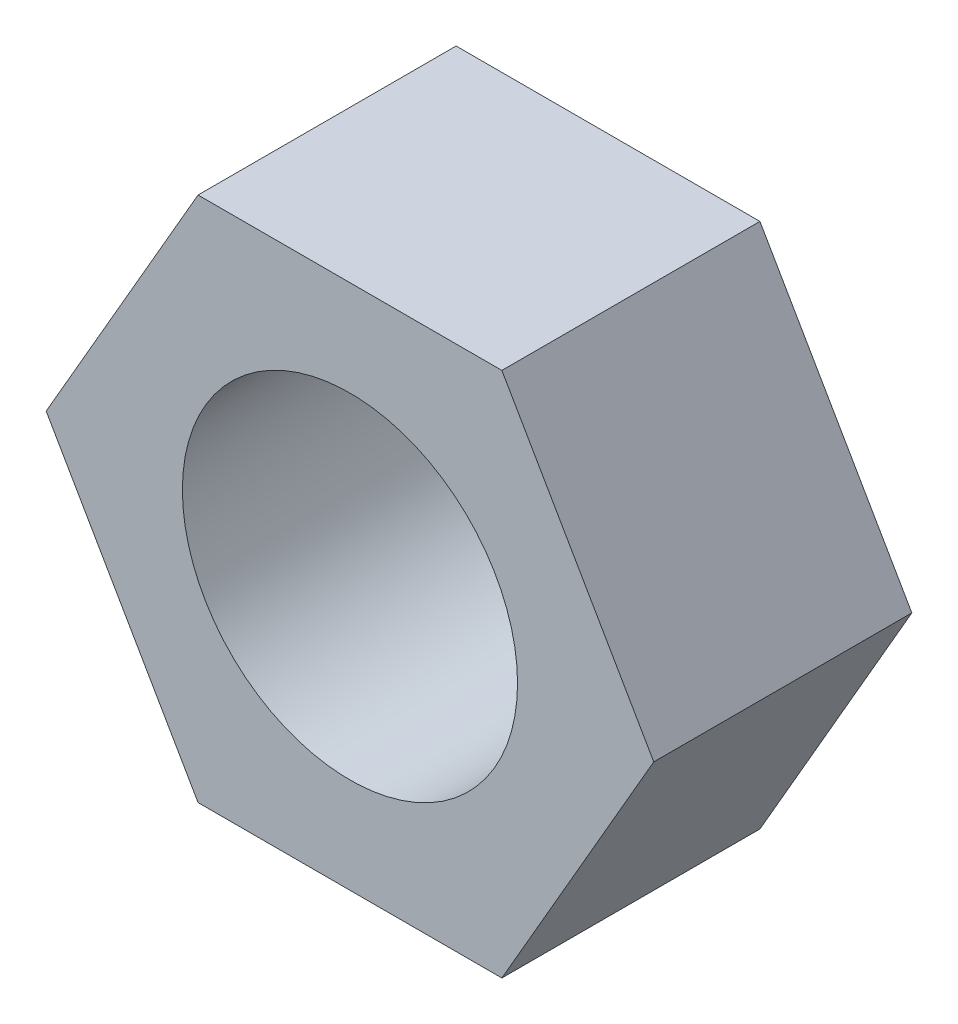
SolidWorks part; units mm, degrees
ref_plane "Front Plane" through (0, 0, 0) normal (0, 0, 1) x (1, 0, 0)
ref_plane "Top Plane" through (0, 0, 0) normal (0, 1, 0) x (1, 0, 0)
ref_plane "Right Plane" through (0, 0, 0) normal (1, 0, 0) x (0, 0, -1)
sketch "Sketch1" plane through (0, 0, 0) normal (0, 0, 1) x (1, 0, 0)
  line L1 (4.5322, 0) -> (2.2661, 3.925)
  line L2 (2.2661, 3.925) -> (-2.2661, 3.925)
  line L3 (-2.2661, 3.925) -> (-4.5322, 0)
  line L4 (-4.5322, 0) -> (-2.2661, -3.925)
  line L5 (-2.2661, -3.925) -> (2.2661, -3.925)
  line L6 (2.2661, -3.925) -> (4.5322, 0)
  circle A0 centre (0, 0) radius 2.5
  circle A1 centre (0, 0) radius 3.925 construction
  dimension "D2" = 5
  dimension "D1" = 7.85
extrude "Boss-Extrude1" add sketch "Sketch1" along normal blind 3.85
